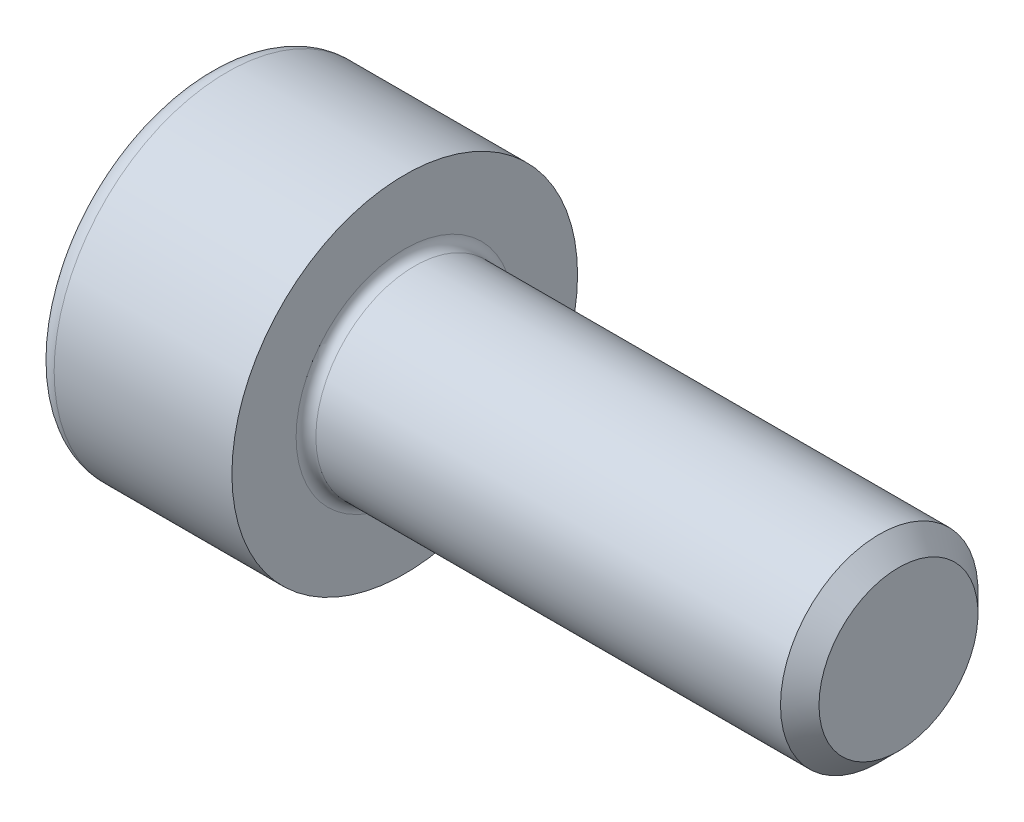
SolidWorks part; units mm, degrees
revolve "Base-Revolve" add sketch "BodySke"
sketch "BodySke" plane through (0, 0, 0) normal (0, 0, 1) x (1, 0, 0)
  line L0 (0, 0) -> (0, 3.5)
  line L1 (0, 3.5) -> (4, 3.5)
  line L2 (4, 3.5) -> (4, 2)
  line L3 (4, 2) -> (13.61, 2)
  line L4 (14, 1.61) -> (14, 0)
  line L5 (14, 0) -> (0, 0)
  line L6 (-31.75, 0) -> (127, 0) construction
  line L8 (14, 1.61) -> (13.61, 2)
  line L10 (14, -1.61) -> (13.61, -2) construction
  line L11 (4.7, 9.525) -> (4.7, 3.175) construction
  line L12 (4, 9.525) -> (4, 3.175) construction
  line L13 (-1.9931, 9.525) -> (-1.9931, 3.175) construction
  dimension "Head_ht" = 4
  dimension "Length" = 10
  dimension "Body_ch_ang" = 45
  dimension "Diameter" = 4
  dimension "Minor_dia" = 3.22
  dimension "Advance" = 0.7
  dimension "Thread_nom" = 10
  dimension "Thread_length" = 15.9931
  dimension "Head_dia" = 7
cosmetic thread "ThreadCosmetic" [suppressed]
fillet "Fillet1" radius 0.2 1 edges at (4, 0, 2)
fillet "Fillet2" radius 0.4 1 edges at (0, 0, 3.5)
ref_plane "Plane1" through (0, 0, 0) normal (0, 0, 1) x (1, 0, 0)
ref_plane "Plane2" through (0, 0, 0) normal (0, 1, 0) x (1, 0, 0)
ref_plane "Plane3" through (0, 0, 0) normal (1, 0, 0) x (0, 0, -1)
sketch "Sketch2" plane through (0, 0, 0) normal (0, 0, 1) x (1, 0, 0)
  line L0 (0, 1.51) -> (2, 1.51)
  line L1 (2, 1.51) -> (2.8718, 0)
  line L2 (-31.75, 0) -> (127, 0) construction
  line L3 (2.8718, 0) -> (0, 0)
  line L4 (0, 0) -> (0, 1.51)
  line L6 (0, 0) -> (47.625, 0) construction
  dimension "D1" = 1.51
  dimension "D2" = 60
  dimension "Depth" = 2
revolve "Hex-PreBroach" cut sketch "Sketch2" angle 360 about L6
sketch "Sketch3" plane through (0, 0, 0) normal (-1, 0, 0) x (0, 0.5, 0.866)
  line L0 (0.8718, 1.51) -> (-0.8718, 1.51)
  line L1 (-0.8718, 1.51) -> (-1.7436, 0)
  line L2 (0.8718, 1.51) -> (1.7436, 0)
  line L3 (0.8718, -1.51) -> (1.7436, 0)
  line L4 (0.8718, -1.51) -> (-0.8718, -1.51)
  line L5 (-0.8718, -1.51) -> (-1.7436, 0)
  dimension "D1" = 1.51
  dimension "D2" = 1.51
  dimension "Hex_size" = 3.02
extrude "Hex" cut sketch "Sketch3" against normal blind 2
sketch "ThdSchSke" plane through (0, 0, 0) normal (0, 0, 1) x (1, 0, 0)
  line L0 (6.1, -1.61) -> (5.8269, -2)
  line L1 (6.1, -1.61) -> (6.3731, -2)
  line L2 (6.3731, -2) -> (6.3731, -2.5)
  line L3 (-3.175, 0) -> (5.1513, 0) construction
  line L4 (0, 3.1) -> (0, -3.1) construction
  line L5 (6.3731, -2.5) -> (5.8269, -2.5)
  line L6 (5.8269, -2.5) -> (5.8269, -2)
  dimension "Thread_minor" = 3.22
  dimension "Diameter" = 4
  dimension "Start" = 6.1
revolve "ThreadSchematic" [suppressed] cut sketch "ThdSchSke" angle 360 about L3
pattern_linear "ThdSchPat" [suppressed]
equation "\"D2@Sketch3\" = \"Hex_size@Sketch3\" / 2"
equation "\"D1@Sketch3\" = \"Hex_size@Sketch3\" / 2"
equation "\"D1@Sketch2\" = \"Hex_size@Sketch3\" / 2"
equation "\"Thread_minor@ThreadCosmetic\"  =  \"Minor_dia@BodySke\""
equation "\"Depth@Sketch2\" =  \"Key_eng@Hex\""
equation "\"Thread_length@ThreadCosmetic\" = ((sgn( (\"Length@BodySke\" - \"Advance@BodySke\" * 3.0) - \"Thread_nom@BodySke\" )-1)*( (\"Length@BodySke\" - \"Advance@BodySke\" * 3.0) - \"Thread_nom@BodySke\" ))/-2+ \"Thread_nom@BodySke\""
equation "\"Thread_minor@ThdSchSke\" = \"Minor_dia@BodySke\""
equation "\"Diameter@ThdSchSke\" = \"Diameter@BodySke\""
equation "\"Overcut@ThdSchSke\" = \"Diameter@BodySke\" * 1.25"
equation "\"Start@ThdSchSke\" = \"Head_ht@BodySke\" + \"Length@BodySke\" - \"Thread_length@ThreadCosmetic\"  '---Non-countersunk---"
equation "\"Num_threads@ThdSchPat\" = int( \"Thread_length@ThreadCosmetic\" / \"Advance@BodySke\" + 0.999 )  + 1"
equation "\"Advance@ThdSchPat\" = \"Thread_length@ThreadCosmetic\" /  (\"Num_threads@ThdSchPat\" - 1) 'relax it"
equation "\"Num_threads@ThdSchPat\" = \"Num_threads@ThdSchPat\" - sgn( \"Num_threads@ThdSchPat\" - 1) '---chamfered tips only---"
